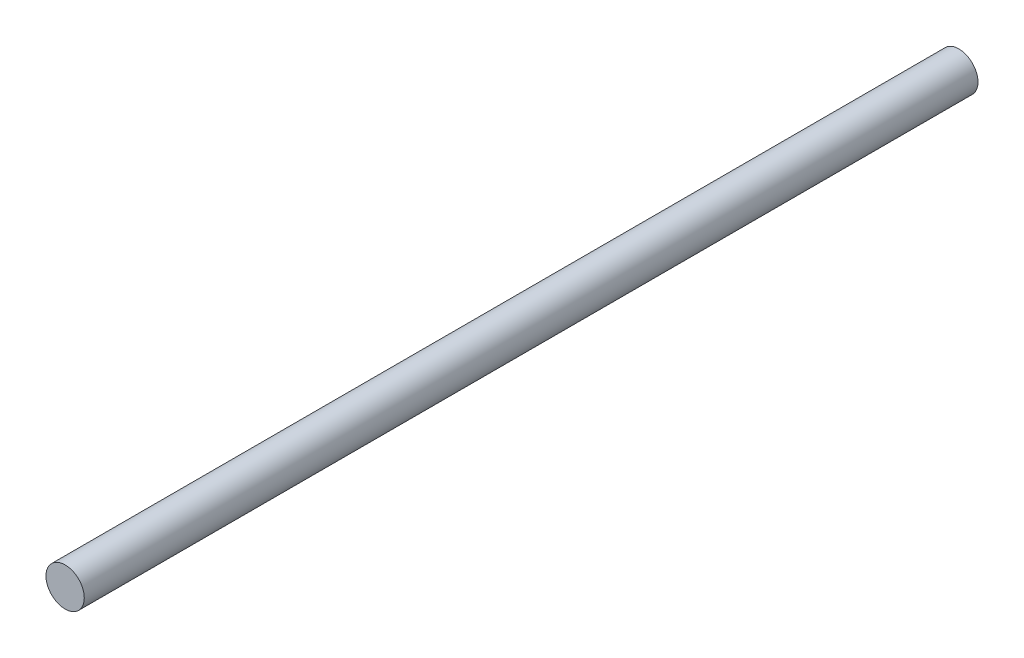
SolidWorks part; units mm, degrees
material "Thornel Mat VMA"
ref_plane "前视基准面" through (0, 0, 0) normal (0, 0, 1) x (1, 0, 0)
ref_plane "上视基准面" through (0, 0, 0) normal (0, 1, 0) x (1, 0, 0)
ref_plane "右视基准面" through (0, 0, 0) normal (1, 0, 0) x (0, 0, -1)
other "Configuration Table"
sketch "草图1" plane through (0, 0, 0) normal (0, 0, 1) x (1, 0, 0)
  circle A0 centre (-1.2505, 4.4588) radius 1.5
  dimension "D1" = 3
extrude "凸台-拉伸1" add sketch "草图1" along normal blind 70
